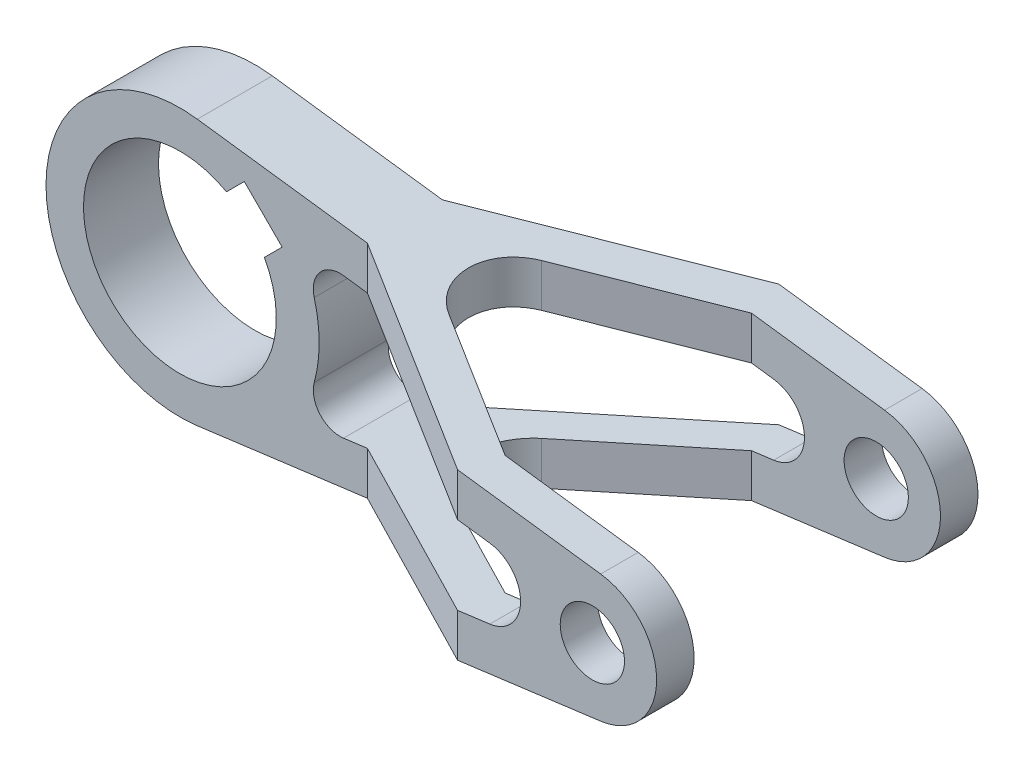
SolidWorks part; units mm, degrees
material "Plain Carbon Steel"
ref_plane "Front Plane" through (0, 0, 0) normal (0, 0, 1) x (1, 0, 0)
ref_plane "Top Plane" through (0, 0, 0) normal (0, 1, 0) x (1, 0, 0)
ref_plane "Right Plane" through (0, 0, 0) normal (1, 0, 0) x (0, 0, -1)
sketch "Sketch1" plane through (0, 0, 0) normal (0, 0, 1) x (1, 0, 0)
  line L0 (3.25, 24.7878) -> (101.56, 11.8982)
  line L1 (3.25, -24.7878) -> (101.56, -11.8982)
  line L2 (100, 0) -> (0, 0) construction
  line L3 (0, 0) -> (30.4552, 30.4552) construction
  line L4 (8.6915, 15.7626) -> (12.0208, 19.0919)
  line L5 (12.0208, 19.0919) -> (19.0919, 12.0208)
  line L6 (19.0919, 12.0208) -> (15.7626, 8.6915)
  arc A0 (8.6915, 15.7626) -> (15.7626, 8.6915) centre (0, 0) ccw
  circle A1 centre (100, 0) radius 6
  arc A2 (3.25, 24.7878) -> (3.25, -24.7878) centre (0, 0) ccw
  arc A3 (101.56, -11.8982) -> (101.56, 11.8982) centre (100, 0) ccw
  dimension "D1" = 18
  dimension "D2" = 25
  dimension "D3" = 12
  dimension "D4" = 12
  dimension "D5" = 100
  dimension "D6" = 45
  dimension "D7" = 10
  dimension "D8" = 22
extrude "Boss-Extrude1" add sketch "Sketch1" along normal mid plane 60
sketch "Sketch2" plane through (0, 0, 30) normal (0, 0, 1) x (1, 0, 0)
  line L0 (0, 0) -> (123.0282, 0) construction
  line L1 (80.858, 6.544) -> (30.5507, 13.1399)
  line L2 (80.858, -6.544) -> (30.5507, -13.1399)
  line L3 (101.56, 11.8982) -> (3.25, 24.7878) construction
  line L4 (3.25, -24.7878) -> (101.56, -11.8982) construction
  arc A0 (25.078, -6.8626) -> (25.078, 6.8626) centre (0, 0) ccw
  arc A1 (80.858, -6.544) -> (80.858, 6.544) centre (80, 0) ccw
  arc A2 (30.5507, -13.1399) -> (25.078, -6.8626) centre (29.9007, -8.1824) cw
  arc A3 (30.5507, 13.1399) -> (25.078, 6.8626) centre (29.9007, 8.1824) ccw
  dimension "D1" = 26
  dimension "D2" = 8
  dimension "D4" = 5
  dimension "D3" = 80
extrude "Cut-Extrude1" cut sketch "Sketch2" against normal through all
sketch "Sketch3" plane through (0, 0, 0) normal (0, 1, 0) x (1, 0, 0)
  line L0 (0, 0) -> (129.2666, 0) construction
  line L1 (-25, 7) -> (35, 7)
  line L2 (-25, 30) -> (-25, -30) construction
  line L3 (35, 7) -> (74.8372, 30)
  line L4 (101.56, 30) -> (3.25, 30) construction
  line L5 (74.8372, 30) -> (112, 30)
  line L6 (112, 30) -> (112, 23)
  line L7 (112, -30) -> (112, 30) construction
  line L8 (112, 23) -> (76.7128, 23)
  line L9 (76.7128, 23) -> (36.8756, 0)
  line L10 (76.7128, -23) -> (36.8756, 0)
  line L11 (112, -23) -> (76.7128, -23)
  line L12 (112, -30) -> (112, -23)
  line L13 (74.8372, -30) -> (112, -30)
  line L14 (35, -7) -> (74.8372, -30)
  line L15 (-25, -7) -> (35, -7)
  line L16 (-25, 7) -> (-25, -7)
  dimension "D1" = 14
  dimension "D2" = 150
  dimension "D3" = 60
  dimension "D4" = 7
  dimension "D5" = 7
extrude "Cut-Extrude2" cut sketch "Sketch3" against normal through all both and the other way through all flip side to cut
fillet "Fillet1" radius 10 2 edges at (36.8756, -16.3449, 0) (36.8756, 16.3449, 0)
